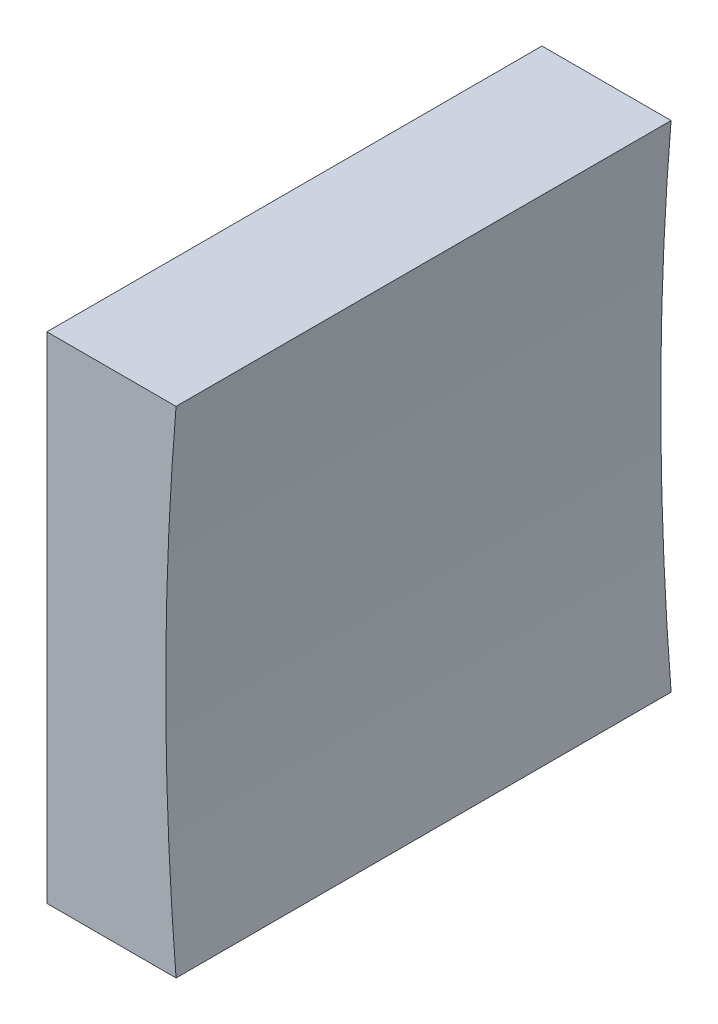
SolidWorks part; units mm, degrees
ref_plane "前视基准面" through (0, 0, 0) normal (0, 0, 1) x (1, 0, 0)
ref_plane "上视基准面" through (0, 0, 0) normal (0, 1, 0) x (1, 0, 0)
ref_plane "右视基准面" through (0, 0, 0) normal (1, 0, 0) x (0, 0, -1)
sketch "草图1" plane through (0, 0, 0) normal (0, 0, 1) x (1, 0, 0)
  line L0 (278.655, 66.8579) -> (298.183, 66.8579) construction
  line L1 (284.7071, 66.8579) -> (284.7071, 79.3579)
  line L2 (284.7071, 79.3579) -> (291.2289, 79.3579)
  line L3 (291.2289, 54.3579) -> (284.7071, 54.3579)
  line L4 (284.7071, 54.3579) -> (284.7071, 66.8579)
  arc A0 (291.2289, 79.3579) -> (291.2289, 54.3579) centre (440.7071, 66.8579) ccw
  dimension "D1" = 150
extrude "凸台-拉伸1" add sketch "草图1" along normal blind 25
